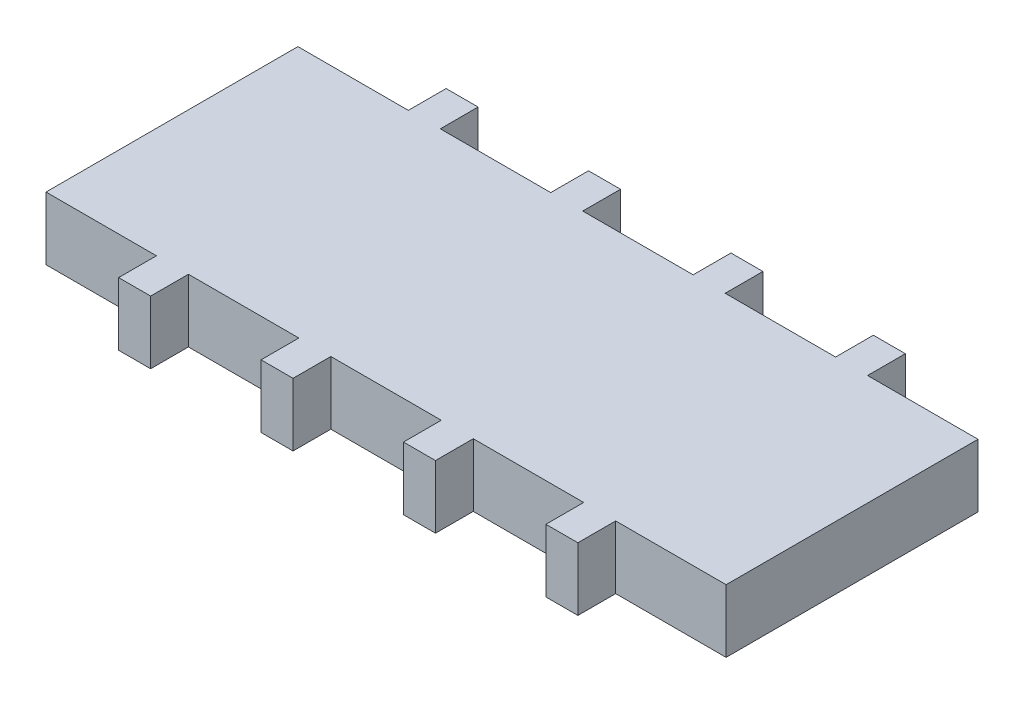
SolidWorks part; units mm, degrees
ref_plane "Front Plane" through (0, 0, 0) normal (0, 0, 1) x (1, 0, 0)
ref_plane "Top Plane" through (0, 0, 0) normal (0, 1, 0) x (1, 0, 0)
ref_plane "Right Plane" through (0, 0, 0) normal (1, 0, 0) x (0, 0, -1)
sketch "Sketch1" plane through (0, 0, 0) normal (0, 1, 0) x (1, 0, 0)
  line L0 (-15.692, 11.5) -> (-6.924, 11.5) construction
  line L1 (-27, 10) -> (27, 10)
  line L2 (-27, 10) -> (-27, -10)
  line L3 (-27, -10) -> (27, -10)
  line L4 (27, 10) -> (27, -10)
  line L5 (-27, 10) -> (27, -10) construction
  line L6 (-27, -10) -> (27, 10) construction
  line L7 (-18.232, 10) -> (-15.692, 10)
  line L8 (-18.232, 10) -> (-18.232, 13)
  line L9 (-18.232, 13) -> (-15.692, 13)
  line L10 (-15.692, 10) -> (-15.692, 13)
  line L11 (-4.384, 10) -> (-6.924, 10)
  line L12 (-4.384, 10) -> (-4.384, 13)
  line L13 (-4.384, 13) -> (-6.924, 13)
  line L14 (-6.924, 10) -> (-6.924, 13)
  line L15 (4.384, 10) -> (6.924, 10)
  line L16 (4.384, 10) -> (4.384, 13)
  line L17 (4.384, 13) -> (6.924, 13)
  line L18 (6.924, 10) -> (6.924, 13)
  line L19 (15.692, 10) -> (18.232, 10)
  line L20 (15.692, 10) -> (15.692, 13)
  line L21 (15.692, 13) -> (18.232, 13)
  line L22 (18.232, 10) -> (18.232, 13)
  line L23 (-18.232, -10) -> (-15.692, -10)
  line L24 (-18.232, -10) -> (-18.232, -13)
  line L25 (-18.232, -13) -> (-15.692, -13)
  line L26 (-15.692, -10) -> (-15.692, -13)
  line L27 (-6.924, -10) -> (-4.384, -10)
  line L28 (-6.924, -10) -> (-6.924, -13)
  line L29 (-6.924, -13) -> (-4.384, -13)
  line L30 (-4.384, -10) -> (-4.384, -13)
  line L31 (4.384, -10) -> (6.924, -10)
  line L32 (4.384, -10) -> (4.384, -13)
  line L33 (4.384, -13) -> (6.924, -13)
  line L34 (6.924, -10) -> (6.924, -13)
  line L35 (15.692, -10) -> (18.232, -10)
  line L36 (15.692, -10) -> (15.692, -13)
  line L37 (15.692, -13) -> (18.232, -13)
  line L38 (18.232, -10) -> (18.232, -13)
  line L39 (-4.384, 11.5) -> (4.384, 11.5) construction
  line L40 (6.924, 11.5) -> (15.692, 11.5) construction
  line L41 (18.232, 11.5) -> (27, 11.5) construction
  line L42 (27, 11.5) -> (27, 10) construction
  line L43 (-18.232, 11.5) -> (-27, 11.5) construction
  line L44 (-27, 11.5) -> (-27, 10) construction
  line L45 (-18.232, -11.5) -> (-27, -11.5) construction
  line L46 (-27, -11.5) -> (-27, -10) construction
  line L47 (-15.692, -11.5) -> (-6.924, -11.5) construction
  line L48 (-4.384, -11.5) -> (4.384, -11.5) construction
  line L49 (6.924, -11.5) -> (15.692, -11.5) construction
  line L50 (18.232, -11.5) -> (27, -11.5) construction
  line L51 (27, -11.5) -> (27, -10) construction
  point P0 (0, 0)
  point P58 (-32.4522, -24.6816)
  point P59 (-4.599, -25.0469)
  point P60 (4.8985, -25.5035)
  point P61 (-13.9139, -25.2296)
  point P62 (-22.4981, -25.3209)
  point P63 (21.9757, -25.2296)
  point P64 (-6.9734, 25.0889)
  point P65 (-14.8271, 24.815)
  point P66 (26.3592, 16.5046)
  point P67 (4.8072, 16.322)
  point P68 (-9.6217, 16.2307)
  point P69 (-8.8436, 21.0908)
  point P70 (3.3417, 20.7861)
  point P71 (15.2224, 20.7252)
  point P72 (-18.6, -21.4241)
  point P73 (0, 0)
  point P74 (-7.0764, 13)
  dimension "D1" = 54
  dimension "D2" = 2.54
  dimension "D3" = 26
  dimension "D4" = 3
extrude "Boss-Extrude1" add sketch "Sketch1" along normal blind 5 contours L4 L1 L2 L3 | L26 L3 L24 L25 | L30 L3 L28 L29 | L34 L3 L32 L33 | L38 L3 L36 L37 | L1 L22 L21 L20 | L1 L18 L17 L16 | L14 L1 L12 L13 | L1 L10 L9 L8
